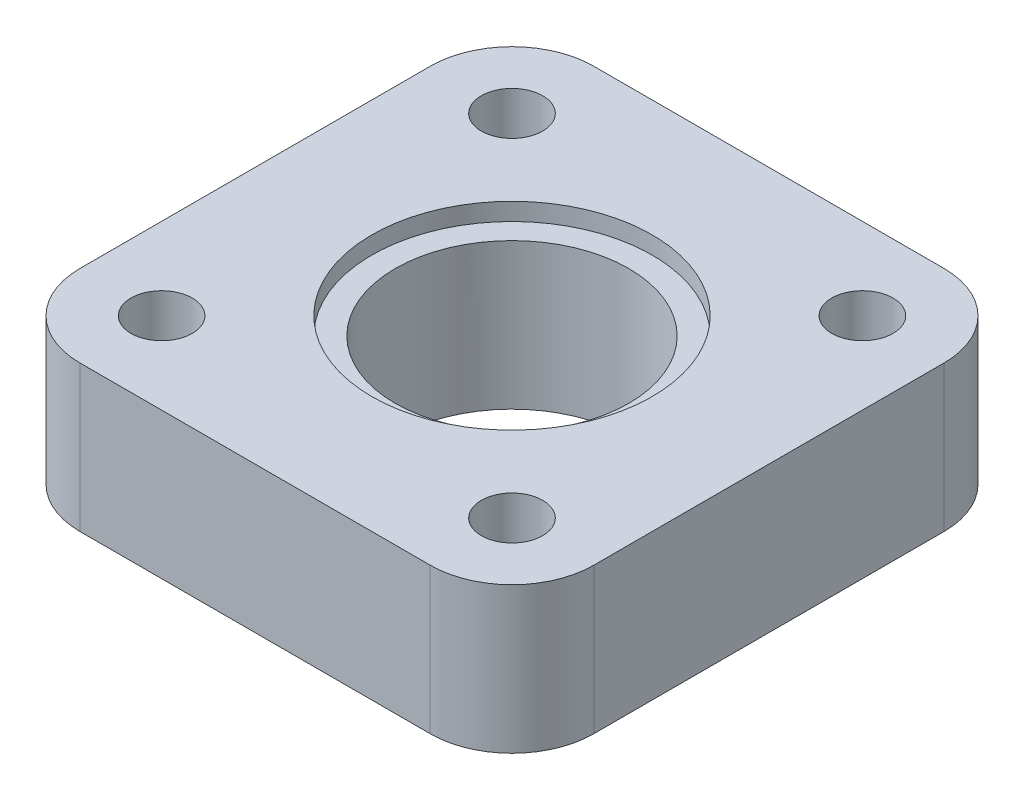
SolidWorks part; units mm, degrees
ref_plane "Plan de face" through (0, 0, 0) normal (0, 0, 1) x (1, 0, 0)
ref_plane "Plan de dessus" through (0, 0, 0) normal (0, 1, 0) x (1, 0, 0)
ref_plane "Plan de droite" through (0, 0, 0) normal (1, 0, 0) x (0, 0, -1)
sketch "Esquisse1" plane through (0, 0, 0) normal (0, 1, 0) x (1, 0, 0)
  line L0 (-30, 30) -> (30, -30) construction
  line L1 (-30, -30) -> (30, -30) construction
  line L2 (-30, -30) -> (-30, 30) construction
  line L3 (-30, 30) -> (30, 30) construction
  line L4 (30, -30) -> (30, 30) construction
  line L5 (-44, 30) -> (-44, -30)
  line L6 (44, 30) -> (44, -30)
  line L7 (-30, -44) -> (30, -44)
  line L8 (-30, 44) -> (30, 44)
  arc A0 (-30, 44) -> (-44, 30) centre (-30, 30) ccw
  arc A1 (-44, -30) -> (-30, -44) centre (-30, -30) ccw
  arc A2 (30, -44) -> (44, -30) centre (30, -30) ccw
  arc A3 (30, 44) -> (44, 30) centre (30, 30) cw
  circle A8 centre (-30, 30) radius 5.25
  circle A9 centre (30, 30) radius 5.25
  circle A10 centre (30, -30) radius 5.25
  circle A11 centre (-30, -30) radius 5.25
  circle A12 centre (0, 0) radius 20
  point P5 (-30, 30)
  point P7 (30, 30)
  point P8 (30, -30)
  point P9 (-30, -30)
  dimension "D3" = 14
  dimension "D5" = 10.5
  dimension "D6" = 40
  dimension "D1" = 60
  dimension "D2" = 60
extrude "Boss.-Extru.1" add sketch "Esquisse1" along normal blind 25
sketch "Esquisse2" plane through (0, 25, 0) normal (0, 1, 0) x (1, 0, 0)
  circle A0 centre (0, 0) radius 24
  dimension "D1" = 48
extrude "Enlèv. mat.-Extru.1" cut sketch "Esquisse2" against normal blind 3
sketch "Esquisse3" plane through (0, 0, 0) normal (0, -1, 0) x (1, 0, 0)
  circle A0 centre (0, 0) radius 23.5
  circle A1 centre (0, 0) radius 20 construction
  circle A2 centre (0, 0) radius 20
extrude "Boss.-Extru.2" add sketch "Esquisse3" along normal blind 3
